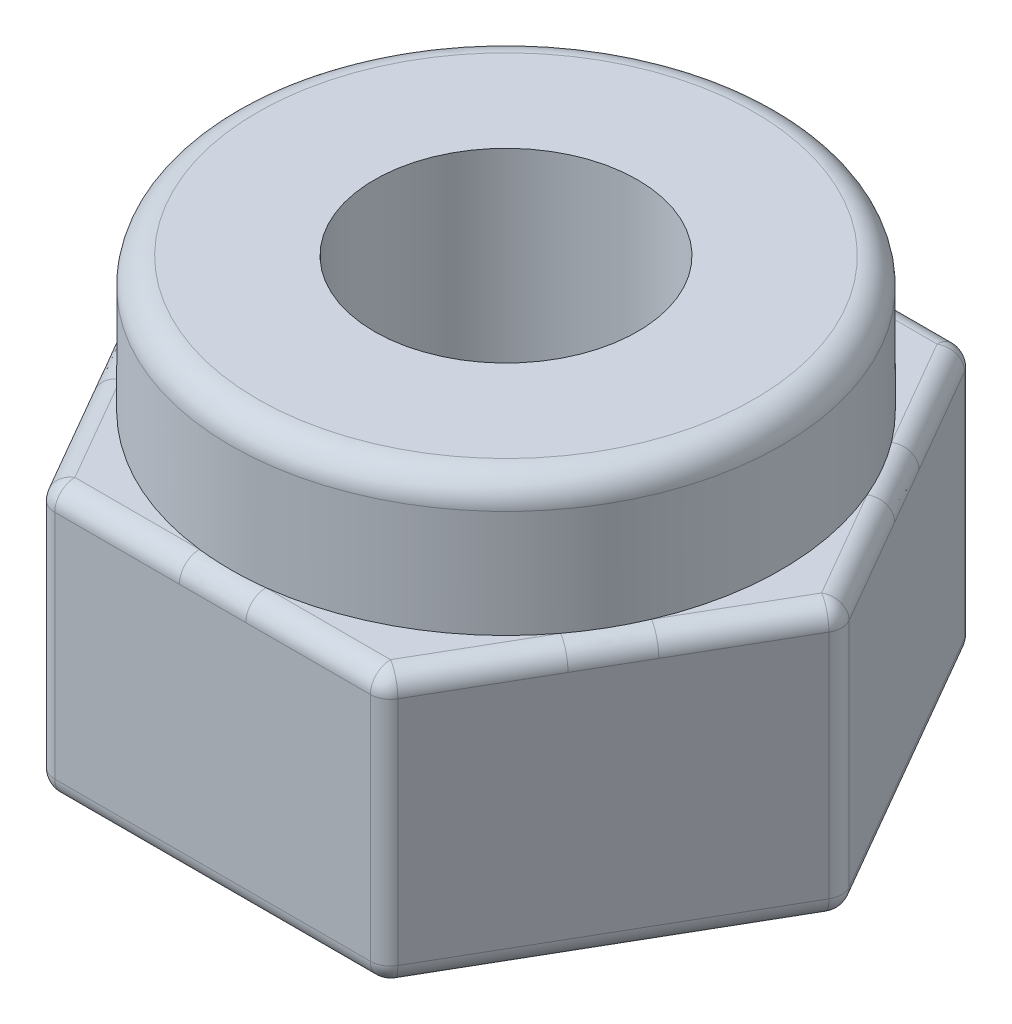
SolidWorks part; units mm, degrees
material "AISI 4130 Steel, normalized at 870C"
ref_plane "Front Plane" through (0, 0, 0) normal (0, 0, 1) x (1, 0, 0)
ref_plane "Top Plane" through (0, 0, 0) normal (0, 1, 0) x (1, 0, 0)
ref_plane "Right Plane" through (0, 0, 0) normal (1, 0, 0) x (0, 0, -1)
ref_plane "Plane1" through (0, -2.54, 0) normal (0, 1, 0) x (-1, 0, 0)
sketch "Sketch1" plane through (0, -2.54, 0) normal (0, 1, 0) x (-1, 0, 0)
  line L0 (3.2042, 5.5499) -> (-3.2042, 5.5499)
  line L1 (-3.2042, 5.5499) -> (-6.4085, 0)
  line L2 (-6.4085, 0) -> (-3.2042, -5.5499)
  line L3 (-3.2042, -5.5499) -> (3.2042, -5.5499)
  line L4 (3.2042, -5.5499) -> (6.4085, 0)
  line L5 (6.4085, 0) -> (3.2042, 5.5499)
  dimension "D1" = 3.2042
  dimension "D2" = 6.4085
  dimension "D3" = 3.2042
extrude "Extrude1" add sketch "Sketch1" against normal blind 5.1308
ref_plane "Plane2" through (0, 0, 0) normal (0, 0, -1) x (-1, 0, 0)
sketch "Sketch2" plane through (0, 0, 0) normal (0, 0, -1) x (-1, 0, 0)
  line L0 (-5.207, -2.54) -> (0, -2.54)
  line L1 (0, -2.54) -> (0, 0)
  line L2 (0, 0) -> (-5.207, 0)
  line L3 (-5.207, 0) -> (-5.207, -2.54)
  line L4 (0, -2.54) -> (0, 0) construction
  dimension "D1" = 5.207
  dimension "D2" = 2.54
revolve "Revolve1" add sketch "Sketch2" angle 360 about L4
hole_wizard "HoleWzd1" positions "Sketch4" profile "Sketch3" legacy
sketch "Sketch4" plane through (0, 0, 0) normal (0, 1, 0) x (-1, 0, 0)
  circle A0 centre (0, 0) radius 5.207 construction
  point P0 (0, 0)
sketch "Sketch3" plane through (0, 0, 0) normal (1, 0, 0) x (0, 0, 1)
  line L0 (0, 0) -> (0, 7.6708)
  line L1 (0, 7.6708) -> (2.4879, 7.6708)
  line L2 (2.4879, 7.6708) -> (2.4879, 0)
  line L3 (2.4879, 0) -> (0, 0)
  line L4 (0, 110) -> (0, -10) construction
  dimension "Diameter" = 4.9759
  dimension "Depth" = 7.6708
fillet "Fillet1" radius 0.381 18 edges at (0, -7.6708, 5.5499) (-3.2042, -5.1054, 5.5499) (0, -2.54, 5.5499) (3.2042, -5.1054, 5.5499) (4.8064, -7.6708, 2.7749) (-4.8064, -7.6708, 2.775) (4.8064, -7.6708, -2.775) (-4.8064, -2.54, 2.775) (-6.4085, -5.1054, 0) (4.8064, -2.54, 2.7749) (6.4085, -5.1054, 0) (0, -7.6708, -5.5499) (-4.8064, -7.6708, -2.7749) (3.2042, -5.1054, -5.5499) (-4.8064, -2.54, -2.7749) (4.8064, -2.54, -2.775) (-3.2042, -5.1054, -5.5499) (0, -2.54, -5.5499)
fillet "Fillet2" radius 0.508 1 edges at (0, 0, 5.207)
